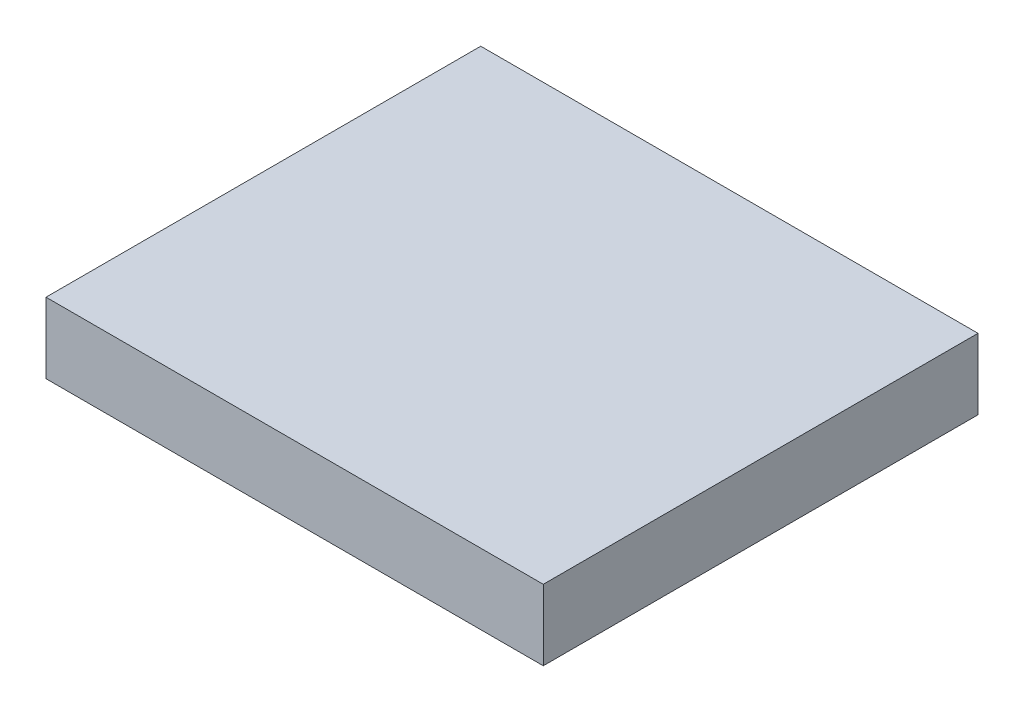
SolidWorks part; units mm, degrees
ref_plane "Front Plane" through (0, 0, 0) normal (0, 0, 1) x (1, 0, 0)
ref_plane "Top Plane" through (0, 0, 0) normal (0, 1, 0) x (1, 0, 0)
ref_plane "Right Plane" through (0, 0, 0) normal (1, 0, 0) x (0, 0, -1)
sketch "Sketch1" plane through (0, 0, 0) normal (0, 1, 0) x (1, 0, 0)
  line L1 (-10.1981, -8.9154) -> (10.1981, -8.9154)
  line L2 (-10.1981, -8.9154) -> (-10.1981, 8.9154)
  line L3 (-10.1981, 8.9154) -> (10.1981, 8.9154)
  line L4 (10.1981, -8.9154) -> (10.1981, 8.9154)
  line L5 (-10.1981, -8.9154) -> (10.1981, 8.9154) construction
  line L6 (-10.1981, 8.9154) -> (10.1981, -8.9154) construction
  point P0 (0, 0)
  dimension "D1" = 20.3962
  dimension "D2" = 17.8308
extrude "Boss-Extrude1" add sketch "Sketch1" along normal blind 2.8956
